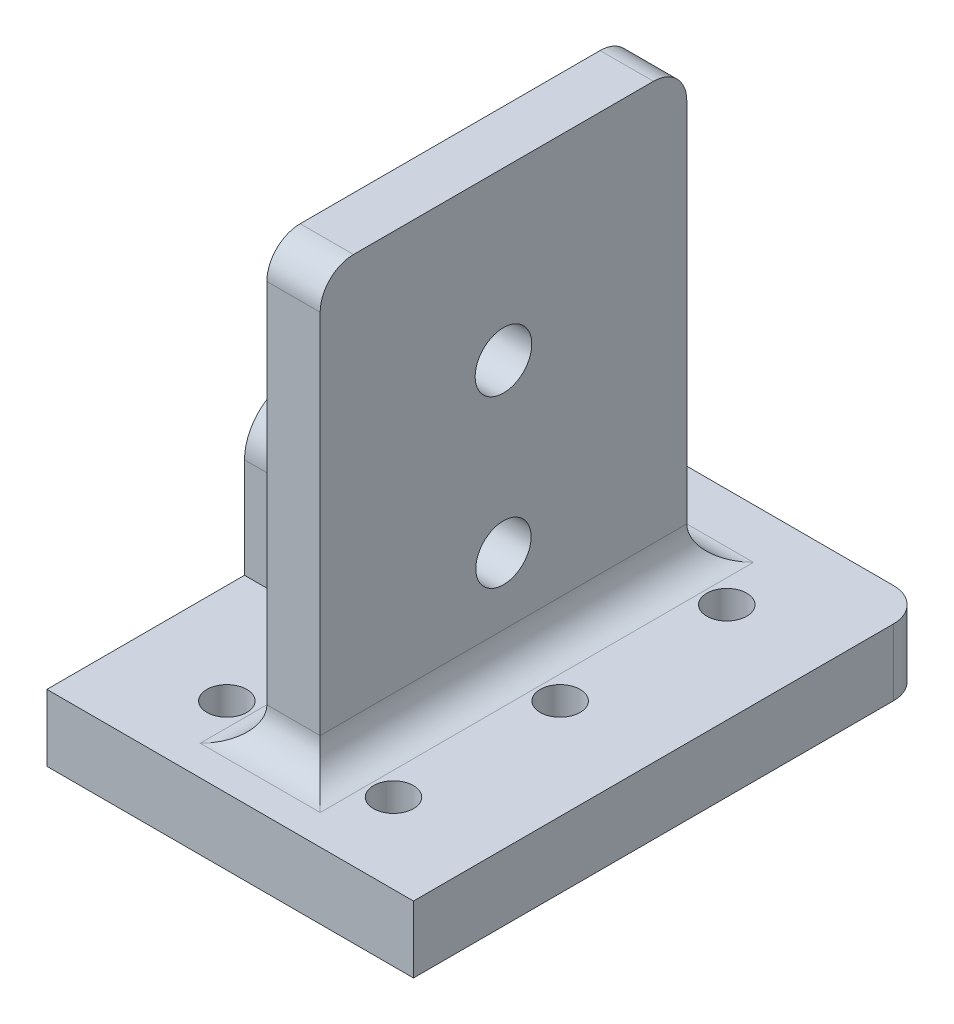
SolidWorks part; units mm, degrees
ref_plane "Front Plane" through (0, 0, 0) normal (0, 0, 1) x (1, 0, 0)
ref_plane "Top Plane" through (0, 0, 0) normal (0, 1, 0) x (1, 0, 0)
ref_plane "Right Plane" through (0, 0, 0) normal (1, 0, 0) x (0, 0, -1)
sketch "Sketch1" plane through (0, 0, 0) normal (0, 1, 0) x (1, 0, 0)
  line L1 (-27.5, 40) -> (27.5, 40)
  line L2 (-27.5, 40) -> (-27.5, -40)
  line L3 (-27.5, -40) -> (27.5, -40)
  line L4 (27.5, 40) -> (27.5, -40)
  line L5 (-27.5, 40) -> (27.5, -40) construction
  line L6 (-27.5, -40) -> (27.5, 40) construction
  point P0 (0, 0)
  dimension "D1" = 55
  dimension "D2" = 80
extrude "Boss-Extrude1" add sketch "Sketch1" along normal blind 10
sketch "Sketch6" plane through (0, 10, 0) normal (0, 1, 0) x (1, 0, 0)
  line L0 (-27.5, -40) -> (27.5, -40) construction
  circle A0 centre (-12.5, -25) radius 1.65
  dimension "D3" = 3.3
  dimension "D1" = 12.5
  dimension "D2" = 15
extrude "Cut-Extrude2" cut sketch "Sketch6" against normal blind 55
pattern_linear "LPattern1" count 3 spacing 25 along (0, 0, -1) of "Cut-Extrude2"
mirror "Mirror3" about plane through (0, 0, 0) normal (1, 0, 0) of "LPattern1", "Cut-Extrude2"
sketch "Sketch8" plane through (0, 10, 0) normal (0, 1, 0) x (1, 0, 0)
  line L1 (-4, 27.5) -> (4, 27.5)
  line L2 (-4, 27.5) -> (-4, -27.5)
  line L3 (-4, -27.5) -> (4, -27.5)
  line L4 (4, 27.5) -> (4, -27.5)
  line L5 (-4, 27.5) -> (4, -27.5) construction
  line L6 (-4, -27.5) -> (4, 27.5) construction
  point P0 (0, 0)
  dimension "D1" = 55
  dimension "D2" = 8
extrude "Boss-Extrude3" add sketch "Sketch8" along normal blind 65
fillet "Fillet3" radius 5 8 edges at (-27.5, 5, -40) (27.5, 5, -40) (0, 75, -27.5) (0, 75, 27.5) (4, 10, 0) (-4, 10, 0) (0, 10, -27.5) (0, 10, 27.5)
sketch "Sketch9" plane through (-4, 0, 0) normal (-1, 0, 0) x (0, 0, 1)
  line L0 (-22.5, 75) -> (22.5, 75) construction
  line L1 (-15.5, 65.5) -> (15.5, 65.5) construction
  line L2 (-15.5, 65.5) -> (-15.5, 34.5) construction
  line L3 (-15.5, 34.5) -> (15.5, 34.5) construction
  line L4 (15.5, 65.5) -> (15.5, 34.5) construction
  line L5 (-15.5, 65.5) -> (15.5, 34.5) construction
  line L6 (-15.5, 34.5) -> (15.5, 65.5) construction
  circle A4 centre (0, 50) radius 4.25
  point P0 (0, 50)
  dimension "D9" = 8.5
  dimension "D1" = 25
  dimension "D2" = 31
  dimension "D3" = 31
  dimension "D4" = 0
extrude "Cut-Extrude3" cut sketch "Sketch9" against normal through all
sketch "Sketch11" plane through (0, 10, 0) normal (0, 1, 0) x (1, 0, 0)
  circle A0 centre (-12.5, -25) radius 3
  dimension "D1" = 6
extrude "Cut-Extrude5" cut sketch "Sketch11" against normal blind 5 and the other way through all
pattern_linear "LPattern2" count 3 spacing 25 along (0, 0, -1) of "Cut-Extrude5"
mirror "Mirror4" about plane through (0, 0, 0) normal (1, 0, 0) of "LPattern2", "Cut-Extrude5"
sketch "Sketch12" plane through (0, 10, 0) normal (0, 1, 0) x (1, 0, 0)
  line L0 (12.5, -25) -> (12.5, -37) construction
  line L1 (12.5, -37) -> (-38.0557, -37)
  line L2 (-38.0557, -37) -> (-38.0557, -44.2873)
  line L3 (-38.0557, -44.2873) -> (40.3693, -44.2873)
  line L4 (40.3693, -44.2873) -> (40.3693, -37)
  line L5 (40.3693, -37) -> (12.5, -37)
  dimension "D1" = 12
extrude "Cut-Extrude6" cut sketch "Sketch12" against normal blind 10
sketch "Sketch13" plane through (-4, 0, 0) normal (-1, 0, 0) x (0, 0, 1)
  line L0 (-7.35, 25) -> (-7.35, 0)
  line L1 (-35, 0) -> (37, 0) construction
  line L2 (-7.35, 0) -> (7.35, 0)
  line L3 (7.35, 0) -> (7.35, 25)
  circle A0 centre (0, 25) radius 4.15
  arc A1 (7.35, 25) -> (-7.35, 25) centre (0, 25) ccw
  circle A3 centre (0, 25) radius 7.35 construction
  point P9 (7.35, 25)
  dimension "D1" = 8.3
  dimension "D2" = 25
  dimension "D3" = 3.2
extrude "Boss-Extrude4" add sketch "Sketch13" along normal up to surface (23.5 mm away) up to face at (-27.5, 5, 1)
sketch "Sketch14" plane through (-4, 0, 0) normal (-1, 0, 0) x (0, 0, 1)
  circle A0 centre (0, 25) radius 4.15
extrude "Cut-Extrude7" cut sketch "Sketch14" against normal blind 20
